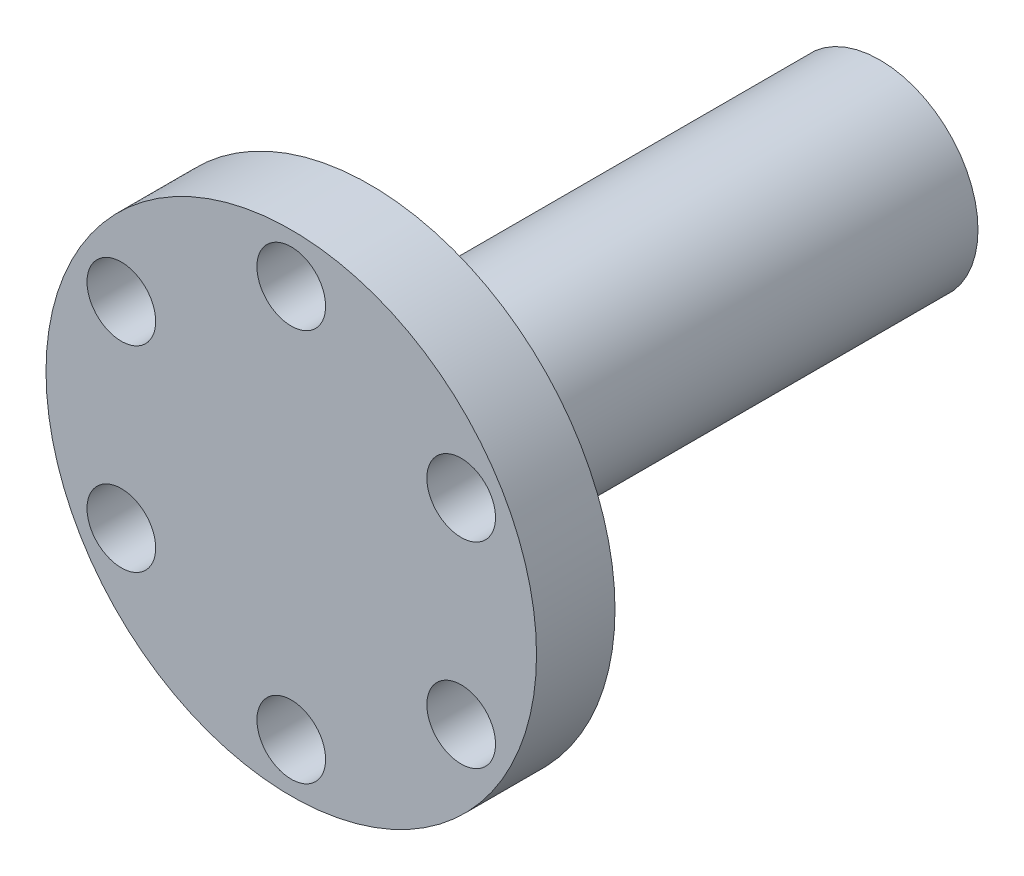
SolidWorks part; units mm, degrees
material "1060 合金"
ref_plane "前基準面" through (0, 0, 0) normal (0, 0, 1) x (1, 0, 0)
ref_plane "上基準面" through (0, 0, 0) normal (0, 1, 0) x (1, 0, 0)
ref_plane "右基準面" through (0, 0, 0) normal (1, 0, 0) x (0, 0, -1)
sketch "草圖1" plane through (0, 0, 0) normal (0, 1, 0) x (1, 0, 0)
  line L0 (0, 76.682) -> (0, -36.7251) construction
  line L1 (0, 0) -> (5, 0)
  line L2 (0, 0) -> (0, 30)
  line L3 (0, 30) -> (5, 30)
  line L4 (5, 0) -> (5, 30)
  line L5 (0, -13.75) -> (0, 13.75) construction
  line L7 (5, 0) -> (12.5, 0)
  line L8 (5, 0) -> (5, 4)
  line L9 (5, 4) -> (12.5, 4)
  line L10 (12.5, 0) -> (12.5, 4)
  dimension "D1" = 10
  dimension "D2" = 30
  dimension "D3" = 25
  dimension "D4" = 0
  dimension "D5" = 4
revolve "旋轉1" add sketch "草圖1" angle 360 about L2
sketch "草圖2" plane through (0, 0, -4) normal (0, 0, -1) x (-1, 0, 0)
  circle A0 centre (0, 0) radius 10 construction
  circle A1 centre (0, 10) radius 1.75
  circle A2 centre (8.6603, 5) radius 1.75
  circle A3 centre (8.6603, -5) radius 1.75
  circle A4 centre (0, -10) radius 1.75
  circle A5 centre (-8.6603, -5) radius 1.75
  circle A6 centre (-8.6603, 5) radius 1.75
  point P18 (0, 0)
  dimension "D1" = 20
  dimension "D2" = 3.5
  dimension "D3" = 6
extrude "除料-伸長1" cut sketch "草圖2" against normal through all
ref_plane "平面1" through (0, 5, 0) normal (0, 1, 0) x (1, 0, 0)
